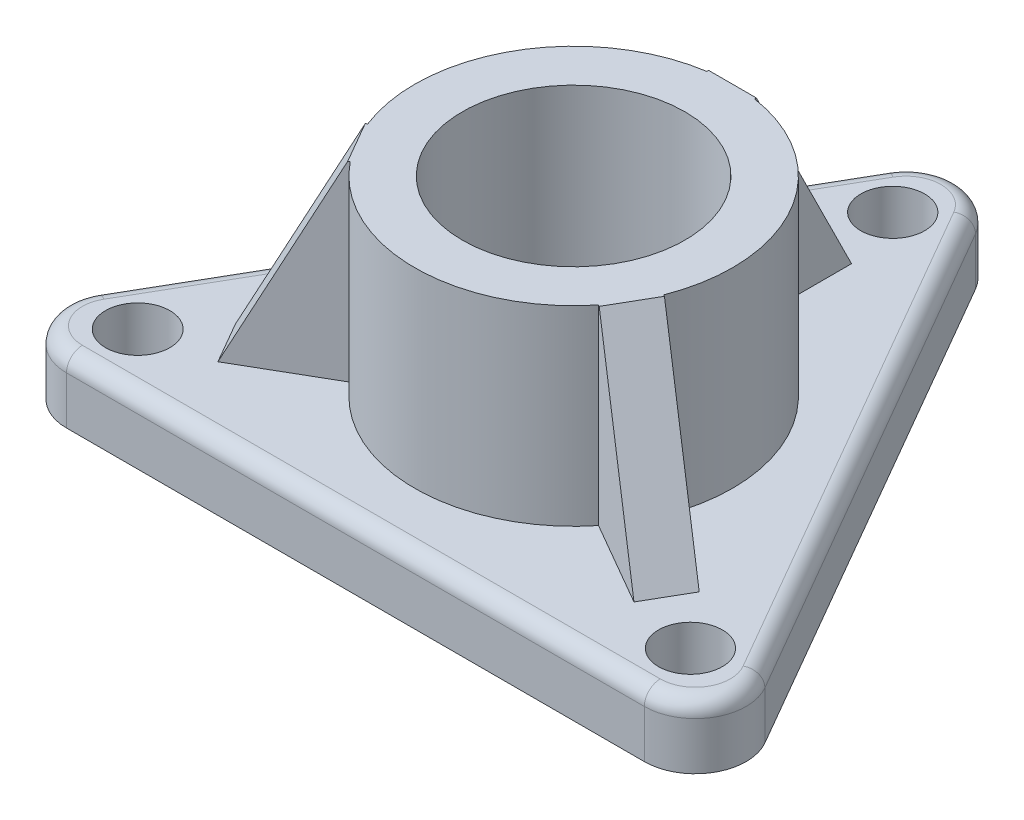
SolidWorks part; units mm, degrees
ref_plane "Front Plane" through (0, 0, 0) normal (0, 0, 1) x (1, 0, 0)
ref_plane "Top Plane" through (0, 0, 0) normal (0, 1, 0) x (1, 0, 0)
ref_plane "Right Plane" through (0, 0, 0) normal (1, 0, 0) x (0, 0, -1)
sketch "Sketch1" plane through (0, 0, 0) normal (0, 1, 0) x (1, 0, 0)
  line L7 (0, 86.5919) -> (-74.9908, -43.296)
  line L8 (-74.9908, -43.296) -> (74.9908, -43.296)
  line L9 (74.9908, -43.296) -> (0, 86.5919)
  circle A3 centre (0, 63.6388) radius 6.3695
  circle A4 centre (55.1128, -31.8194) radius 6.3644
  circle A5 centre (-55.1128, -31.8194) radius 6.4132
extrude "Boss-Extrude2" add sketch "Sketch1" along normal blind 12.7
fillet "Fillet5" radius 9.906 1 edges at (-74.9908, 6.35, 43.296)
fillet "Fillet6" radius 10.16 1 edges at (74.9908, 6.35, 43.296)
fillet "Fillet7" radius 10.16 1 edges at (0, 6.35, -86.5919)
fillet "Fillet8" radius 3.175 6 edges at (0, 12.7, -76.4319) (37.4954, 12.7, -21.648) (-37.6054, 12.7, -21.4575) (-66.412, 12.7, 38.343) (-0.22, 12.7, 43.296) (66.192, 12.7, 38.216)
sketch "Sketch2" plane through (0, 12.7, 0) normal (0, 1, 0) x (1, 0, 0)
  circle A0 centre (0, 0) radius 31.6964
extrude "Boss-Extrude3" add sketch "Sketch2" along normal blind 38.1
sketch "Sketch3" plane through (0, 50.8, 0) normal (0, 1, 0) x (1, 0, 0)
  circle A0 centre (0, 0) radius 22.1936
extrude "Cut-Extrude1" cut sketch "Sketch3" against normal blind 31.75
sketch "Sketch4" plane through (0, 12.7, 0) normal (0, 1, 0) x (1, 0, 0)
  line L0 (0, 0) -> (-55.1128, -31.8194)
  line L1 (0, 0) -> (0, 63.6388)
  line L2 (0, 0) -> (55.1128, -31.8194)
ref_plane "Plane1" through (-27.4499, 0, 15.8482) normal (-0.866, 0, 0.5) x (0.5, 0, 0.866)
sketch "Sketch5" plane through (-27.4499, 0, 15.8482) normal (-0.866, 0, 0.5) x (0.5, 0, 0.866)
  line L0 (0, 12.7) -> (0, 50.8)
  line L1 (0, 12.7) -> (55.1128, 12.7) construction
  line L2 (31.6964, 50.8) -> (-31.6964, 50.8) construction
ref_plane "Plane2" through (0, 0, 0) normal (-0.5, 0, -0.866) x (-0.866, 0, 0.5)
sketch "Sketch6" plane through (0, 0, 0) normal (-0.5, 0, -0.866) x (-0.866, 0, 0.5)
  line L0 (31.6964, 12.7) -> (50.6555, 12.7)
  line L1 (-29.6435, 12.7) -> (70.1454, 12.7) construction
  line L2 (50.6555, 12.7) -> (31.6964, 50.8)
  line L3 (31.6964, 50.8) -> (28.0669, 50.8)
  line L4 (31.6964, 50.8) -> (-31.6964, 50.8) construction
  line L5 (28.0669, 50.8) -> (28.0669, 12.7)
  line L6 (28.0669, 12.7) -> (31.6964, 12.7)
extrude "Boss-Extrude4" add sketch "Sketch6" along normal blind 4.7625
sketch "Sketch8" plane through (-2.3813, 0, -4.1244) normal (-0.5, 0, -0.866) x (-0.866, 0, 0.5)
  line L0 (31.0053, 12.5789) -> (50.6555, 12.7)
  line L1 (50.6555, 12.7) -> (31.6964, 50.8)
  line L2 (31.6964, 50.8) -> (27.1487, 50.8)
  line L3 (31.6964, 50.8) -> (-31.6964, 50.8) construction
  line L4 (27.1487, 50.8) -> (27.1487, 12.5789)
  line L5 (27.1487, 12.5789) -> (31.0053, 12.5789)
extrude "Boss-Extrude6" add sketch "Sketch8" against normal blind 9.525
pattern_circular "CirPattern1" count 3 over 360 about axis through (0, 0, 0) along (0, 1, 0) of "Boss-Extrude6"
